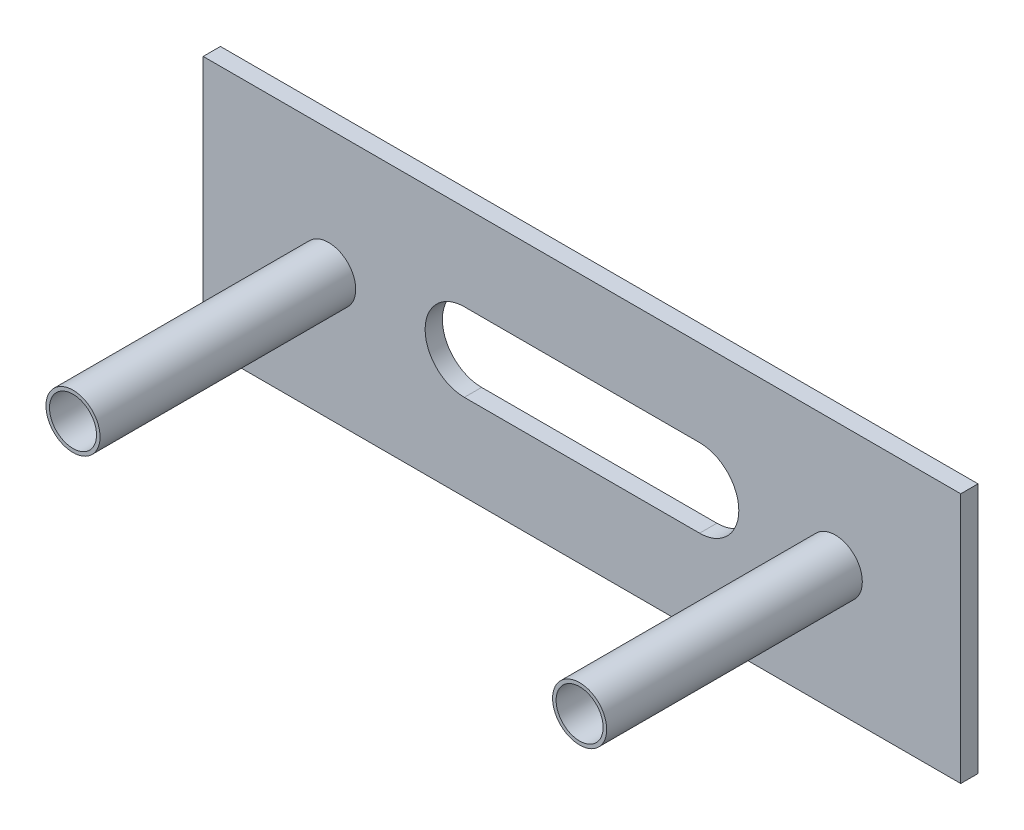
SolidWorks part; units mm, degrees
ref_plane "Plan de face" through (0, 0, 0) normal (0, 0, 1) x (1, 0, 0)
ref_plane "Plan de dessus" through (0, 0, 0) normal (0, 1, 0) x (1, 0, 0)
ref_plane "Plan de droite" through (0, 0, 0) normal (1, 0, 0) x (0, 0, -1)
sketch "Esquisse1" plane through (0, 0, 0) normal (0, 0, 1) x (1, 0, 0)
  line L1 (-47.6288, 18.2599) -> (48.9712, 18.2599)
  line L2 (-47.6288, 18.2599) -> (-47.6288, -13.7401)
  line L3 (-47.6288, -13.7401) -> (48.9712, -13.7401)
  line L4 (48.9712, 18.2599) -> (48.9712, -13.7401)
  dimension "D1" = 96.6
  dimension "D2" = 32
extrude "Boss.-Extru.1" add sketch "Esquisse1" along normal blind 2.2
sketch "Esquisse6" plane through (0, 0, 2.2) normal (0, 0, 1) x (1, 0, 0)
  line L0 (-47.6288, 18.2599) -> (-47.6288, -13.7401) construction
  line L3 (48.9712, 18.2599) -> (-47.6288, 18.2599) construction
  line L4 (48.9712, -13.7401) -> (48.9712, 18.2599) construction
  circle A0 centre (-31.6288, 2.2599) radius 3.45
  circle A1 centre (32.9712, 2.2599) radius 3.45
  dimension "D1" = 6.9
  dimension "D4" = 6.9
  dimension "D2" = 16
  dimension "D3" = 16
  dimension "D5" = 16
  dimension "D6" = 16
extrude "Boss.-Extru.2" add sketch "Esquisse6" along normal blind 32.6
sketch "Esquisse7" plane through (0, 0, 34.8) normal (0, 0, 1) x (1, 0, 0)
  line L0 (-14.3288, 2.2599) -> (15.6712, 2.2599) construction
  line L1 (-47.6288, 18.2599) -> (-47.6288, -13.7401) construction
  line L3 (48.9712, 18.2599) -> (-47.6288, 18.2599) construction
  line L4 (48.9712, -13.7401) -> (48.9712, 18.2599) construction
  line L5 (-47.6288, -13.7401) -> (48.9712, -13.7401) construction
  line L7 (-14.3288, 7.2599) -> (15.6712, 7.2599)
  line L8 (-14.3288, -2.7401) -> (15.6712, -2.7401)
  circle A0 centre (-31.6288, 2.2599) radius 3
  circle A1 centre (32.9712, 2.2599) radius 3
  arc A5 (-14.3288, 7.2599) -> (-14.3288, -2.7401) centre (-14.3288, 2.2599) ccw
  arc A6 (15.6712, -2.7401) -> (15.6712, 7.2599) centre (15.6712, 2.2599) ccw
  point P16 (0.6712, 2.2599)
  dimension "D1" = 6
  dimension "D4" = 6
  dimension "D7" = 48.3
  dimension "D2" = 16
  dimension "D3" = 16
  dimension "D5" = 16
  dimension "D6" = 16
  dimension "D8" = 30
  dimension "D9" = 10
  dimension "D10" = 16
extrude "Enlèv. mat.-Extru.1" cut sketch "Esquisse7" against normal through all
